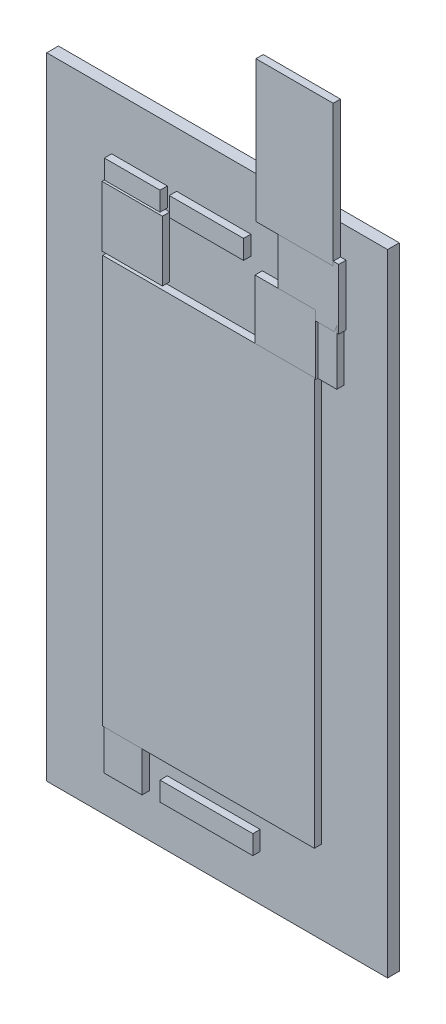
SolidWorks part; units mm, degrees
ref_plane "Front Plane" through (0, 0, 0) normal (0, 0, 1) x (1, 0, 0)
ref_plane "Top Plane" through (0, 0, 0) normal (0, 1, 0) x (1, 0, 0)
ref_plane "Right Plane" through (0, 0, 0) normal (1, 0, 0) x (0, 0, -1)
sketch "Sketch1" plane through (0, 0, 0) normal (0, 0, 1) x (1, 0, 0)
  line L0 (-10.16, 0) -> (36.5, 0)
  line L1 (36.5, 0) -> (36.5, 86.35)
  line L2 (36.5, 86.35) -> (-10.16, 86.35)
  line L3 (-10.16, 86.35) -> (-10.16, 0)
extrude "BOARD" add sketch "Sketch1" along normal blind 1.6 separate body
ref_plane "Plane1" through (0, 0, 1.6) normal (0, 0, 1) x (1, 0, 0)
sketch "Sketch2" plane through (0, 0, 1.6) normal (0, 0, 1) x (1, 0, 0)
  line L0 (-1.6002, 67.6148) -> (-1.6002, 75.8952)
  line L1 (-1.6002, 75.8952) -> (6.6802, 75.8952)
  line L2 (6.6802, 75.8952) -> (6.6802, 67.6148)
  line L3 (6.6802, 67.6148) -> (-1.6002, 67.6148)
extrude "E3_5-8-1" add sketch "Sketch2" along normal blind 1 separate body
sketch "Sketch3" plane through (0, 0, 1.6) normal (0, 0, 1) x (1, 0, 0)
  line L0 (30.8102, 73.9648) -> (22.5298, 73.9648)
  line L1 (22.5298, 73.9648) -> (22.5298, 82.2452)
  line L2 (22.5298, 82.2452) -> (30.8102, 82.2452)
  line L3 (30.8102, 82.2452) -> (30.8102, 73.9648)
extrude "E3_5-8-2" add sketch "Sketch3" along normal blind 1 separate body
sketch "Sketch4" plane through (0, 0, 1.6) normal (0, 0, 1) x (1, 0, 0)
  line L0 (19.3548, 66.9798) -> (19.3548, 75.2602)
  line L1 (19.3548, 75.2602) -> (27.6352, 75.2602)
  line L2 (27.6352, 75.2602) -> (27.6352, 66.9798)
  line L3 (27.6352, 66.9798) -> (19.3548, 66.9798)
extrude "E3_5-8-3" add sketch "Sketch4" along normal blind 1 separate body
sketch "Sketch5" plane through (0, 0, 1.6) normal (0, 0, 1) x (1, 0, 0)
  line L0 (17.78, 76.2) -> (7.62, 76.2)
  line L1 (7.62, 76.2) -> (7.62, 78.8162)
  line L2 (7.62, 78.8162) -> (17.78, 78.8162)
  line L3 (17.78, 78.8162) -> (17.78, 76.2)
extrude "DO41-10-1" add sketch "Sketch5" along normal blind 1 separate body
sketch "Sketch6" plane through (0, 0, 1.6) normal (0, 0, 1) x (1, 0, 0)
  line L0 (19.4818, 100.965) -> (30.0482, 100.965)
  line L1 (30.0482, 100.965) -> (30.0482, 81.661)
  line L2 (30.0482, 81.661) -> (19.4818, 81.661)
  line L3 (19.4818, 81.661) -> (19.4818, 100.965)
extrude "TO220H-1" add sketch "Sketch6" along normal blind 1 separate body
sketch "Sketch7" plane through (0, 0, 1.6) normal (0, 0, 1) x (1, 0, 0)
  line L0 (3.8862, 5.8928) -> (-1.3462, 5.8928)
  line L1 (-1.3462, 5.8928) -> (-1.3462, 11.811)
  line L2 (-1.3462, 11.811) -> (3.8862, 11.811)
  line L3 (3.8862, 11.811) -> (3.8862, 5.8928)
extrude "DIL04-1" add sketch "Sketch7" along normal blind 1 separate body
sketch "Sketch8" plane through (0, 0, 1.6) normal (0, 0, 1) x (1, 0, 0)
  line L0 (16.51, 33.147) -> (3.5052, 33.147)
  line L1 (3.5052, 33.147) -> (3.5052, 35.433)
  line L2 (3.5052, 35.433) -> (16.51, 35.433)
  line L3 (16.51, 35.433) -> (16.51, 33.147)
extrude "0207_12-1" add sketch "Sketch8" along normal blind 1 separate body
sketch "Sketch9" plane through (0, 0, 1.6) normal (0, 0, 1) x (1, 0, 0)
  line L0 (16.51, 40.767) -> (3.5052, 40.767)
  line L1 (3.5052, 40.767) -> (3.5052, 43.053)
  line L2 (3.5052, 43.053) -> (16.51, 43.053)
  line L3 (16.51, 43.053) -> (16.51, 40.767)
extrude "0207_12-2" add sketch "Sketch9" along normal blind 1 separate body
sketch "Sketch10" plane through (0, 0, 1.6) normal (0, 0, 1) x (1, 0, 0)
  line L0 (30.5562, 74.93) -> (30.5562, 67.31)
  line L1 (30.5562, 67.31) -> (27.94, 67.31)
  line L2 (27.94, 67.31) -> (27.94, 74.93)
  line L3 (27.94, 74.93) -> (30.5562, 74.93)
extrude "1X03-1" add sketch "Sketch10" along normal blind 1 separate body
sketch "Sketch11" plane through (0, 0, 1.6) normal (0, 0, 1) x (1, 0, 0)
  line L0 (-1.27, 78.8162) -> (6.35, 78.8162)
  line L1 (6.35, 78.8162) -> (6.35, 76.2)
  line L2 (6.35, 76.2) -> (-1.27, 76.2)
  line L3 (-1.27, 76.2) -> (-1.27, 78.8162)
extrude "1X03-2" add sketch "Sketch11" along normal blind 1 separate body
sketch "Sketch12" plane through (0, 0, 1.6) normal (0, 0, 1) x (1, 0, 0)
  line L0 (19.05, 6.2738) -> (6.35, 6.2738)
  line L1 (6.35, 6.2738) -> (6.35, 8.89)
  line L2 (6.35, 8.89) -> (19.05, 8.89)
  line L3 (19.05, 8.89) -> (19.05, 6.2738)
extrude "1X05-1" add sketch "Sketch12" along normal blind 1 separate body
sketch "Sketch13" plane through (0, 0, 1.6) normal (0, 0, 1) x (1, 0, 0)
  line L0 (27.47, 11.36) -> (-1.5, 11.36)
  line L1 (-1.5, 11.36) -> (-1.5, 67.16)
  line L2 (-1.5, 67.16) -> (27.47, 67.16)
  line L3 (27.47, 67.16) -> (27.47, 11.36)
extrude "MODULE_ESP32-DEVKITC-32U-1" add sketch "Sketch13" along normal blind 1 separate body
